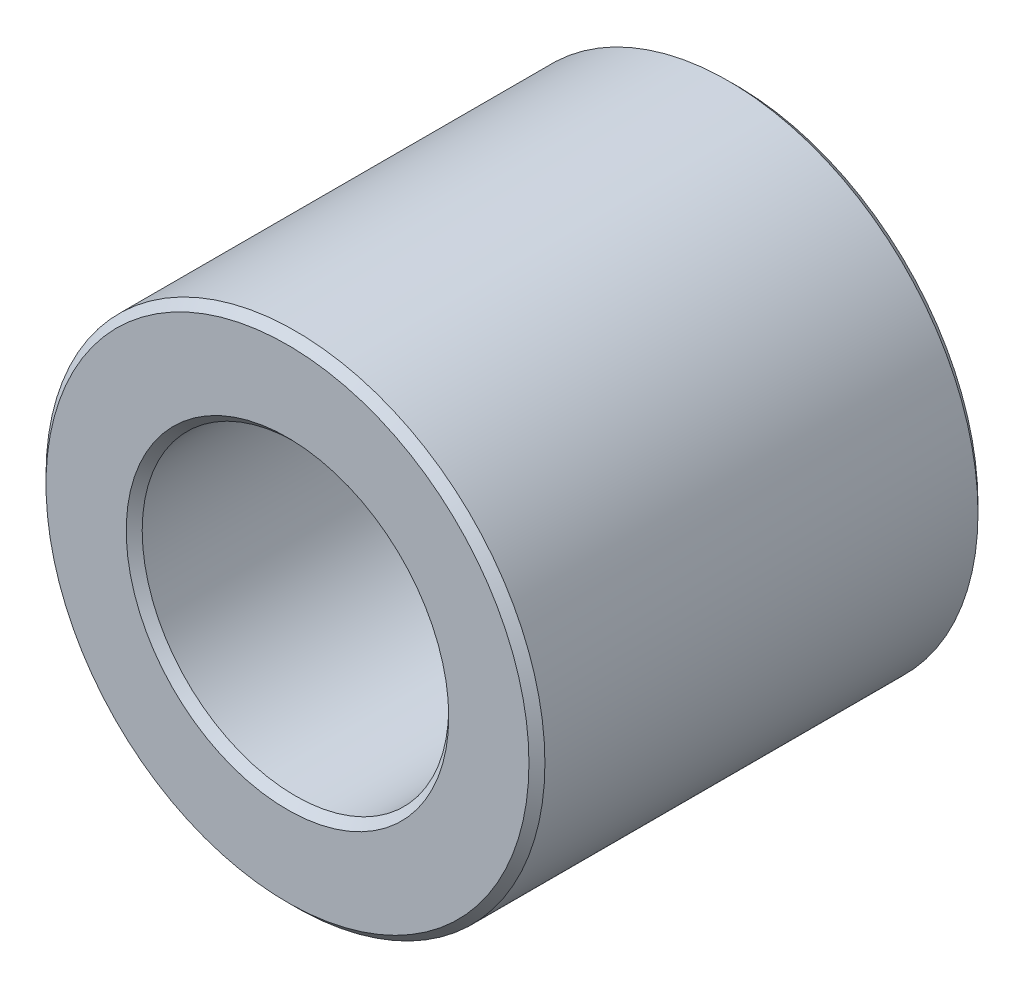
SolidWorks part; units mm, degrees
ref_plane "Front Plane" through (0, 0, 0) normal (0, 0, 1) x (1, 0, 0)
ref_plane "Top Plane" through (0, 0, 0) normal (0, 1, 0) x (1, 0, 0)
ref_plane "Right Plane" through (0, 0, 0) normal (1, 0, 0) x (0, 0, -1)
sketch "Sketch1" plane through (0, 0, 0) normal (0, 0, 1) x (1, 0, 0)
  circle A0 centre (0, 0) radius 3.9688
  circle A1 centre (0, 0) radius 2.4384
  dimension "OD" = 7.9375
  dimension "ID" = 4.8768
sketch "Sketch2" plane through (0, 0, 0) normal (1, 0, 0) x (0, 0, -1)
  line L0 (-3.5719, 0) -> (3.5719, 0) construction
  point P0 (3.5719, 3.9688)
  point P3 (0, 0)
  point P6 (-3.5719, 3.9688)
  point P7 (0, 3.9688)
  dimension "Length" = 7.1437
sketch "Sketch3" plane through (0, 0, 0) normal (0, 0, 1) x (1, 0, 0)
  circle A0 centre (0, 0) radius 3.9688 construction
  circle A1 centre (0, 0) radius 2.4384 construction
  circle A2 centre (0, 0) radius 3.9688
  circle A3 centre (0, 0) radius 2.4384
extrude "Boss-Extrude1" add sketch "Sketch3" against normal up to vertex (3.5719 mm away) and the other way up to vertex (3.5719 mm away) up to point (0, 0, -3.5719) other way up to point (0, 0, 3.5719)
chamfer "Chamfer1" distance 0.127 angle 45 4 edges at (3.9688, 0, 3.5719) (3.9688, 0, -3.5719) (2.4384, 0, -3.5719) (2.4384, 0, 3.5719)
sketch "Sketch4" plane through (0, 0, 0) normal (1, 0, 0) x (0, 0, -1)
  line L0 (3.4449, 2.4384) -> (-3.4449, 2.4384)
  line L1 (-3.4449, -2.4384) -> (3.4449, -2.4384)
  line L2 (-3.4449, -2.4384) -> (3.4449, -2.4384)
  line L3 (3.4449, 2.4384) -> (-3.4449, 2.4384)
